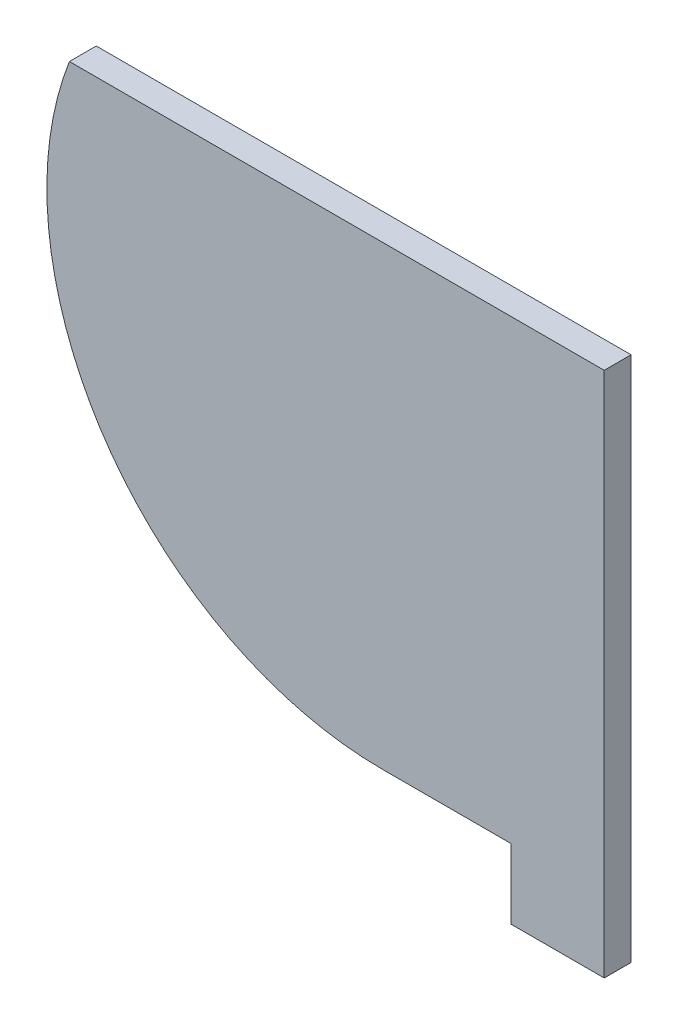
SolidWorks part; units mm, degrees
ref_plane "Front Plane" through (0, 0, 0) normal (0, 0, 1) x (1, 0, 0)
ref_plane "Top Plane" through (0, 0, 0) normal (0, 1, 0) x (1, 0, 0)
ref_plane "Right Plane" through (0, 0, 0) normal (1, 0, 0) x (0, 0, -1)
sketch "Sketch1" plane through (0, 0, 0) normal (0, 0, 1) x (1, 0, 0)
  line L12 (0, 0) -> (0, -85)
  line L13 (-41.2806, -85) -> (0, -85)
  line L14 (0, 0) -> (-99.5901, 0)
  arc A3 (-99.5901, 0) -> (-41.2806, -85) centre (-41.2806, -22.5) ccw
  dimension "D1" = 62.5
  dimension "D2" = 41.2806
  dimension "D3" = 85
extrude "Boss-Extrude1" add sketch "Sketch1" along normal blind 5
sketch "Sketch2" plane through (0, 0, 5) normal (0, 0, 1) x (1, 0, 0)
  line L0 (-17.35, -85) -> (-17.35, -98)
  line L1 (-17.35, -85) -> (0, -85)
  line L2 (-17.35, -98) -> (0, -98)
  line L3 (0, -85) -> (0, -98)
  line L4 (2.8398, -98) -> (-26.3802, -98) construction
  line L8 (-41.2806, -85) -> (0, -85) construction
  line L12 (0.87, -87.011) -> (0.87, -110.6927) construction
  line L13 (0.87, -110) -> (0.87, -107) construction
  line L14 (-18.35, -88.5135) -> (-18.35, -110.6927) construction
  line L15 (-18.35, -107) -> (-18.35, -110) construction
  line L17 (0, -85) -> (0, 0) construction
  dimension "D1" = 1
extrude "Boss-Extrude2" add sketch "Sketch2" against normal blind 5
